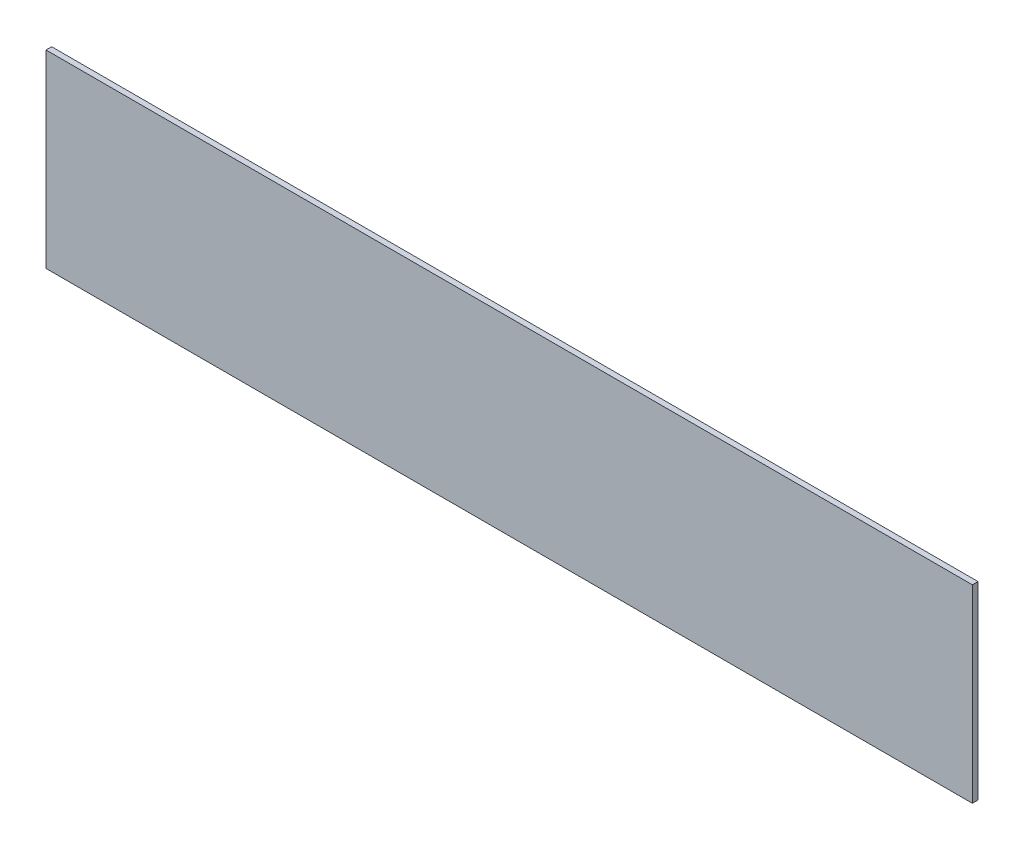
SolidWorks part; units mm, degrees
material "PE High Density"
ref_plane "Front Plane" through (0, 0, 0) normal (0, 0, 1) x (1, 0, 0)
ref_plane "Top Plane" through (0, 0, 0) normal (0, 1, 0) x (1, 0, 0)
ref_plane "Right Plane" through (0, 0, 0) normal (1, 0, 0) x (0, 0, -1)
sketch "Sketch1" plane through (0, 0, 0) normal (0, 0, 1) x (1, 0, 0)
  line L1 (-520.7, 106.3625) -> (520.7, 106.3625)
  line L2 (-520.7, 106.3625) -> (-520.7, -106.3625)
  line L3 (-520.7, -106.3625) -> (520.7, -106.3625)
  line L4 (520.7, 106.3625) -> (520.7, -106.3625)
  line L5 (-520.7, 106.3625) -> (520.7, -106.3625) construction
  line L6 (-520.7, -106.3625) -> (520.7, 106.3625) construction
  circle A3 centre (-216.662, -4.7625) radius 5.1594
  circle A4 centre (-170.434, -4.7625) radius 5.3578
  circle A5 centre (170.434, -4.7625) radius 5.3578
  circle A6 centre (216.662, -4.7625) radius 5.3578
  circle A12 centre (344.17, 42.8625) radius 5.3578
  circle A13 centre (-344.17, 42.8625) radius 5.3578
  point P0 (0, 0)
  dimension "D3" = 10.7156
  dimension "D4" = 10.3187
  dimension "D11" = 10.7156
  dimension "D12" = 10.7156
  dimension "D15" = 63.5
  dimension "D16" = 10.7156
  dimension "D17" = 46.228
  dimension "D18" = 304.038
  dimension "D20" = 63.5
  dimension "D21" = 10.7156
  dimension "D1" = 212.725
  dimension "D2" = 1041.4
  dimension "D5" = 176.53
  dimension "D6" = 176.53
  dimension "D7" = 101.6
  dimension "D8" = 101.6
  dimension "D9" = 101.6
  dimension "D10" = 101.6
  dimension "D13" = 304.038
  dimension "D14" = 46.228
extrude "Boss-Extrude1" add sketch "Sketch1" along normal blind 6.35 contours L2 L1 L4 L3
sketch "Sketch4" plane through (0, 0, 6.35) normal (0, 0, 1) x (1, 0, 0)
  line L2 (-520.7, 106.3625) -> (-520.7, -106.3625) construction
  line L5 (-520.7, -106.3625) -> (520.7, -106.3625) construction
  line L6 (520.7, 106.3625) -> (520.7, -106.3625) construction
  line L7 (-520.7, 106.3625) -> (520.7, 106.3625) construction
  circle A0 centre (476.25, 74.6125) radius 8.382
  circle A1 centre (418.3103, 74.6125) radius 8.382
  circle A2 centre (-476.25, 74.6125) radius 8.382
  circle A3 centre (-418.338, 74.6125) radius 8.382
  circle A4 centre (476.25, -84.1375) radius 8.382
  circle A5 centre (418.3103, -84.1375) radius 8.382
  circle A6 centre (-476.25, -84.1375) radius 8.382
  circle A7 centre (-418.3103, -84.1375) radius 8.382
  dimension "D2" = 16.764
  dimension "D3" = 16.764
  dimension "D4" = 16.764
  dimension "D5" = 16.764
  dimension "D6" = 16.764
  dimension "D7" = 16.764
  dimension "D8" = 16.764
  dimension "D9" = 16.764
  dimension "D1" = 102.362
  dimension "D10" = 22.225
  dimension "D11" = 44.45
  dimension "D12" = 102.3897
  dimension "D13" = 44.45
  dimension "D14" = 102.3897
  dimension "D15" = 22.225
  dimension "D16" = 44.45
  dimension "D17" = 102.3897
  dimension "D18" = 31.75
  dimension "D19" = 44.45
  dimension "D20" = 31.75
extrude "Cut-Extrude1" [suppressed] cut sketch "Sketch4" against normal through all
sketch "Sketch5" plane through (0, 0, 6.35) normal (0, 0, 1) x (1, 0, 0)
  line L0 (-520.7, 106.3625) -> (-520.7, -106.3625) construction
  line L1 (520.7, 106.3625) -> (520.7, -106.3625) construction
  line L2 (-520.7, 106.3625) -> (520.7, 106.3625) construction
  circle A0 centre (-216.662, -4.7625) radius 5.1594
  circle A1 centre (-170.434, -4.7625) radius 5.3578
  circle A2 centre (170.434, -4.7625) radius 5.3578
  circle A3 centre (216.662, -4.7625) radius 5.3578
  circle A4 centre (344.17, 42.8625) radius 5.3578
  circle A5 centre (-344.17, 42.8625) radius 5.3578
  dimension "D1" = 176.53
  dimension "D2" = 176.53
  dimension "D3" = 63.5
  dimension "D4" = 63.5
extrude "Cut-Extrude2" [suppressed] cut sketch "Sketch5" against normal through all
fillet "Fillet1" [suppressed] radius 6.35
